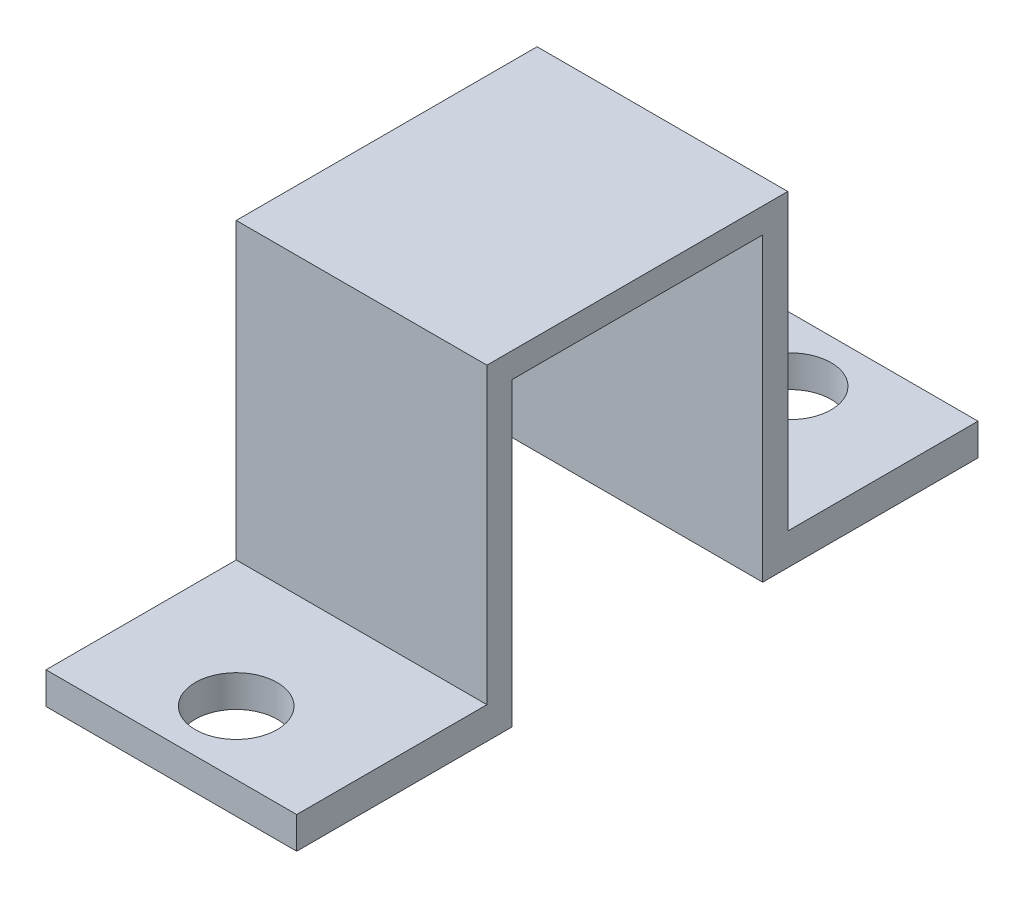
SolidWorks part; units mm, degrees
material "ABS"
ref_plane "Front Plane" through (0, 0, 0) normal (0, 0, 1) x (1, 0, 0)
ref_plane "Top Plane" through (0, 0, 0) normal (0, 1, 0) x (1, 0, 0)
ref_plane "Right Plane" through (0, 0, 0) normal (1, 0, 0) x (0, 0, -1)
sketch "Sketch1" plane through (0, 0, 0) normal (1, 0, 0) x (0, 0, -1)
  line L0 (10.828, 0.032) -> (2.239, 0.032)
  line L2 (2.239, 0.032) -> (2.239, 1.302)
  line L3 (2.239, 1.302) -> (9.828, 1.302)
  line L6 (9.828, 1.302) -> (9.828, 13.032)
  line L7 (9.828, 13.032) -> (14.543, 13.032)
  line L8 (10.828, 0.032) -> (10.828, 12.032)
  line L9 (14.543, 13.032) -> (21.828, 13.032)
  line L11 (10.828, 12.032) -> (20.828, 12.032)
  line L14 (20.828, 12.032) -> (20.828, 0.032)
  line L15 (20.828, 0.032) -> (29.417, 0.032)
  line L16 (21.828, 13.032) -> (21.828, 1.302)
  line L19 (21.828, 1.302) -> (29.417, 1.302)
  line L20 (29.417, 0.032) -> (29.417, 1.302)
  dimension "D1" = 27.178
  dimension "D2" = 12
  dimension "D3" = 10
  dimension "D4" = 1
  dimension "D5" = 1
  dimension "D6" = 1
  dimension "D7" = 1.27
  dimension "D9" = 1.27
extrude "Boss-Extrude1" add sketch "Sketch1" along normal blind 10
hole_wizard "#30 (0.1285) Diameter Hole1" positions "3DSketch1" profile "Sketch2" hole size "#30" standard "ANSI Inch" end condition through all
sketch3d "3DSketch1"
  line L0 (10, 1.302, -29.417) -> (0, 1.302, -29.417) construction
  line L1 (10, 1.302, -2.239) -> (0, 1.302, -2.239) construction
  line L2 (10, 1.302, -29.417) -> (10, 1.302, -21.828) construction
  line L3 (10, 1.302, -9.828) -> (10, 1.302, -2.239) construction
  point P0 (5.047, 1.302, -26.877)
  point P2 (5.047, 1.302, -4.779)
  dimension "D1" = 2.54
  dimension "D2" = 2.54
  dimension "D3" = 4.953
  dimension "D4" = 4.953
sketch "Sketch2" plane through (5.047, 1.302, -26.877) normal (1, 0, 0) x (0, 0, 1)
  line L0 (0, 0) -> (0, 1.27)
  line L1 (0, 1.27) -> (1.6319, 1.27)
  line L2 (1.6319, 1.27) -> (1.6319, 0)
  line L5 (1.6319, 0) -> (0, 0)
  line L11 (0, -6.35) -> (0, 107.95) construction
  dimension "Thru Hole Dia." = 3.2639
  dimension "Thru Hole Depth" = 1.27
